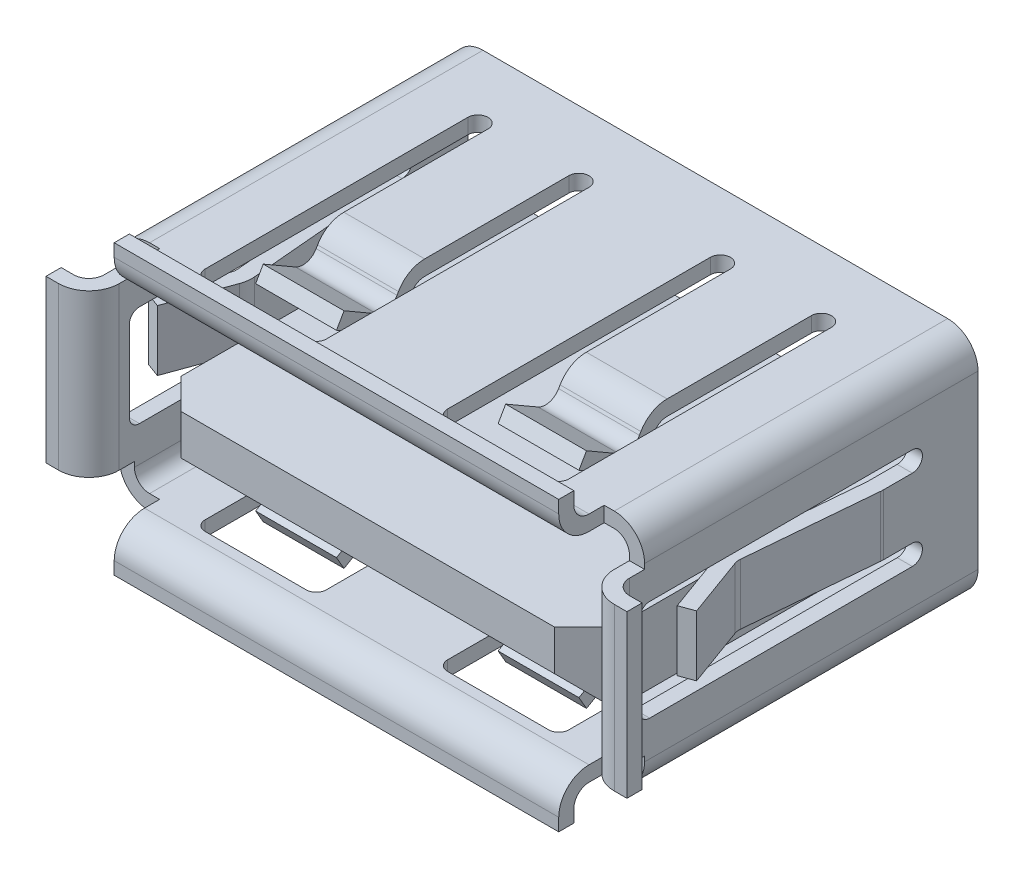
SolidWorks part; units mm, degrees
ref_plane "Front Plane" through (0, 0, 0) normal (0, 0, 1) x (1, 0, 0)
ref_plane "Top Plane" through (0, 0, 0) normal (0, 1, 0) x (1, 0, 0)
ref_plane "Right Plane" through (0, 0, 0) normal (1, 0, 0) x (0, 0, -1)
sketch "Sketch10" plane through (0, 0, 0) normal (0, 0, 1) x (1, 0, 0)
  line L0 (-22.3107, 0) -> (0, 0) construction
  line L1 (0, 8.8149) -> (0, -8.8149) construction
  line L2 (-5.842, 2.54) -> (5.842, 2.54)
  line L3 (-5.842, 2.921) -> (5.842, 2.921)
  line L4 (-6.604, 2.159) -> (-6.604, -2.159)
  line L5 (-5.842, -2.921) -> (5.842, -2.921)
  line L6 (6.604, 2.159) -> (6.604, -2.159)
  line L7 (6.223, 2.159) -> (6.223, -2.159)
  line L8 (-5.842, -2.54) -> (5.842, -2.54)
  line L9 (-6.223, 2.159) -> (-6.223, -2.159)
  arc A0 (-6.604, 2.159) -> (-5.842, 2.921) centre (-5.842, 2.159) cw
  arc A1 (-5.842, -2.921) -> (-6.604, -2.159) centre (-5.842, -2.159) cw
  arc A2 (6.604, -2.159) -> (5.842, -2.921) centre (5.842, -2.159) cw
  arc A3 (5.842, 2.921) -> (6.604, 2.159) centre (5.842, 2.159) cw
  arc A4 (-6.223, 2.159) -> (-5.842, 2.54) centre (-5.842, 2.159) cw
  arc A5 (5.842, 2.54) -> (6.223, 2.159) centre (5.842, 2.159) cw
  arc A6 (6.223, -2.159) -> (5.842, -2.54) centre (5.842, -2.159) cw
  arc A7 (-5.842, -2.54) -> (-6.223, -2.159) centre (-5.842, -2.159) cw
  point P13 (-6.604, -2.921)
  point P16 (6.604, -2.921)
  dimension "D6" = 0.762
  dimension "D2" = 13.208
  dimension "D3" = 6.604
  dimension "D4" = 5.842
  dimension "D5" = 2.921
  dimension "D7" = 0.381
extrude "Extrude6" add sketch "Sketch10" along normal blind 8.382
sketch "Sketch11" plane through (0, 0, 8.382) normal (0, 0, 1) x (1, 0, 0)
  line L0 (-6.604, 2.159) -> (-6.604, -2.159) construction
  line L1 (-6.604, 2.032) -> (-6.223, 2.032)
  line L2 (-6.604, 2.032) -> (-6.604, -2.032)
  line L3 (-6.604, -2.032) -> (-6.223, -2.032)
  line L4 (-6.223, 2.032) -> (-6.223, -2.032)
  line L5 (-6.223, 2.159) -> (-6.223, -2.159) construction
  line L6 (-5.842, -2.54) -> (5.842, -2.54) construction
  line L7 (-5.588, -2.54) -> (5.588, -2.54)
  line L8 (-5.588, -2.54) -> (-5.588, -2.921)
  line L9 (-5.588, -2.921) -> (5.588, -2.921)
  line L10 (5.588, -2.54) -> (5.588, -2.921)
  line L11 (-5.842, -2.921) -> (5.842, -2.921) construction
  line L12 (5.842, 2.921) -> (-5.842, 2.921) construction
  line L13 (-5.588, 2.921) -> (5.588, 2.921)
  line L14 (-5.588, 2.921) -> (-5.588, 2.54)
  line L15 (-5.588, 2.54) -> (5.588, 2.54)
  line L16 (5.588, 2.921) -> (5.588, 2.54)
  line L17 (5.842, 2.54) -> (-5.842, 2.54) construction
  line L18 (6.223, -2.159) -> (6.223, 2.159) construction
  line L19 (6.223, 2.032) -> (6.604, 2.032)
  line L20 (6.223, 2.032) -> (6.223, -2.032)
  line L21 (6.223, -2.032) -> (6.604, -2.032)
  line L22 (6.604, 2.032) -> (6.604, -2.032)
  line L23 (6.604, -2.159) -> (6.604, 2.159) construction
  dimension "D1" = 11.176
  dimension "D2" = 4.064
  dimension "D3" = 0.889
  dimension "D4" = 1.016
extrude "Extrude7" add sketch "Sketch11" along normal blind 0.254
sketch "Sketch12" plane through (5.588, 0, 0) normal (1, 0, 0) x (0, 0, -1)
  line L0 (-9.525, 3.302) -> (-9.525, 3.6195)
  line L1 (-9.144, 3.302) -> (-9.144, 3.6195)
  line L2 (-9.525, 3.6195) -> (-9.144, 3.6195)
  line L3 (-9.525, -3.302) -> (-9.525, -3.6195)
  line L4 (-8.382, 2.54) -> (-8.382, 2.921)
  line L5 (-8.382, 2.921) -> (-8.636, 2.921)
  line L6 (-8.636, 2.921) -> (-8.636, 2.54)
  line L7 (-8.636, 2.54) -> (-8.382, 2.54)
  line L8 (-8.382, 2.54) -> (-8.382, 2.921)
  line L9 (-8.382, 2.921) -> (-8.763, 2.921)
  line L10 (-8.382, -2.921) -> (-8.382, -2.54)
  line L11 (-8.763, 2.54) -> (-8.382, 2.54)
  line L12 (-8.382, -2.54) -> (-8.636, -2.54)
  line L13 (-8.636, -2.54) -> (-8.636, -2.921)
  line L14 (-8.636, -2.921) -> (-8.382, -2.921)
  line L15 (-8.382, -2.921) -> (-8.382, -2.54)
  line L16 (-8.382, -2.54) -> (-8.763, -2.54)
  line L17 (-9.144, -3.302) -> (-9.144, -3.6195)
  line L18 (-8.763, -2.921) -> (-8.382, -2.921)
  line L19 (-9.525, -3.6195) -> (-9.144, -3.6195)
  line L20 (0, 0) -> (-11.5715, 0) construction
  line L21 (0, -2.159) -> (0, 2.159) construction
  arc A0 (-8.763, 2.54) -> (-9.525, 3.302) centre (-8.763, 3.302) cw
  arc A1 (-8.763, -2.54) -> (-9.525, -3.302) centre (-8.763, -3.302) ccw
  arc A2 (-8.763, 2.921) -> (-9.144, 3.302) centre (-8.763, 3.302) cw
  arc A3 (-8.763, -2.921) -> (-9.144, -3.302) centre (-8.763, -3.302) ccw
  dimension "D7" = 0.762
  dimension "D8" = 0.381
  dimension "D3" = 1.0795
  dimension "D4" = 1.0795
  dimension "D5" = 0.381
  dimension "D6" = 9.525
  dimension "D1" = 0
  dimension "D2" = 0
extrude "Extrude8" add sketch "Sketch12" against normal blind 11.176
sketch "Sketch13" plane through (0, 2.032, 0) normal (0, 1, 0) x (-1, 0, 0)
  line L0 (-6.985, 9.144) -> (-7.3025, 9.144)
  line L1 (-7.3025, 9.144) -> (-7.3025, 9.525)
  line L2 (-7.3025, 9.525) -> (-6.985, 9.525)
  line L3 (6.985, 9.144) -> (7.3025, 9.144)
  line L4 (6.223, 8.382) -> (6.604, 8.382)
  line L5 (6.604, 8.382) -> (6.604, 8.636)
  line L6 (6.604, 8.636) -> (6.223, 8.636)
  line L7 (6.223, 8.636) -> (6.223, 8.382)
  line L8 (6.223, 8.382) -> (6.604, 8.382)
  line L9 (6.604, 8.382) -> (6.604, 8.763)
  line L10 (7.3025, 9.144) -> (7.3025, 9.525)
  line L11 (6.223, 8.763) -> (6.223, 8.382)
  line L12 (-6.604, 8.382) -> (-6.223, 8.382)
  line L13 (-6.223, 8.382) -> (-6.223, 8.636)
  line L14 (-6.223, 8.636) -> (-6.604, 8.636)
  line L15 (-6.604, 8.636) -> (-6.604, 8.382)
  line L16 (-6.604, 8.382) -> (-6.223, 8.382)
  line L17 (-6.223, 8.382) -> (-6.223, 8.763)
  line L18 (7.3025, 9.525) -> (6.985, 9.525)
  line L19 (-6.604, 8.763) -> (-6.604, 8.382)
  line L20 (5.588, 9.525) -> (-5.588, 9.525) construction
  arc A0 (-6.985, 9.144) -> (-6.604, 8.763) centre (-6.985, 8.763) cw
  arc A1 (6.985, 9.144) -> (6.604, 8.763) centre (6.985, 8.763) ccw
  arc A2 (-6.223, 8.763) -> (-6.985, 9.525) centre (-6.985, 8.763) ccw
  arc A3 (6.985, 9.525) -> (6.223, 8.763) centre (6.985, 8.763) ccw
  point P26 (6.223, 9.525)
  dimension "D6" = 0.381
  dimension "D7" = 0.762
  dimension "D3" = 0.381
  dimension "D4" = 1.0795
  dimension "D5" = 1.0795
  dimension "D1" = 0
  dimension "D2" = 0
extrude "Extrude9" add sketch "Sketch13" against normal up to surface (4.064 mm away) up to face at (-6.4611, -2.032, 8.5725)
sketch "Sketch14" plane through (0, 2.921, 0) normal (0, 1, 0) x (-1, 0, 0)
  line L0 (0, 0) -> (0, 2.9776) construction
  line L1 (-2.032, 1.651) -> (-2.032, 2.159)
  line L2 (4.572, 1.651) -> (4.572, 8.255)
  line L3 (4.318, 8.509) -> (1.778, 8.509)
  line L4 (1.524, 1.651) -> (1.524, 8.255)
  line L5 (-3.048, 8.509) -> (-3.048, 0.7388) construction
  line L6 (-1.524, 1.651) -> (-1.524, 8.255)
  line L7 (-1.778, 8.509) -> (-4.318, 8.509)
  line L8 (-4.572, 1.651) -> (-4.572, 8.255)
  line L10 (3.048, 8.509) -> (3.048, 0.7388) construction
  line L11 (-2.032, 2.159) -> (-4.064, 2.159)
  line L12 (5.588, 9.525) -> (-5.588, 9.525) construction
  line L13 (-4.064, 2.159) -> (-4.064, 1.651)
  line L14 (4.064, 1.651) -> (4.064, 2.159)
  line L15 (4.064, 2.159) -> (2.032, 2.159)
  line L16 (2.032, 2.159) -> (2.032, 1.651)
  arc A0 (-4.572, 8.255) -> (-4.318, 8.509) centre (-4.318, 8.255) cw
  arc A1 (-1.524, 8.255) -> (-1.778, 8.509) centre (-1.778, 8.255) ccw
  arc A2 (-2.032, 1.651) -> (-1.524, 1.651) centre (-1.778, 1.651) ccw
  arc A3 (-4.572, 1.651) -> (-4.064, 1.651) centre (-4.318, 1.651) ccw
  arc A4 (2.032, 1.651) -> (1.524, 1.651) centre (1.778, 1.651) cw
  arc A5 (4.572, 1.651) -> (4.064, 1.651) centre (4.318, 1.651) cw
  arc A6 (4.318, 8.509) -> (4.572, 8.255) centre (4.318, 8.255) cw
  arc A7 (1.524, 8.255) -> (1.778, 8.509) centre (1.778, 8.255) cw
  dimension "D6" = 7.112
  dimension "D1" = 0.254
  dimension "D7" = 0.762
  dimension "D2" = 1.016
  dimension "D3" = 3.048
  dimension "D4" = 6.096
  dimension "D5" = 3.048
extrude "Cut-Extrude4" cut sketch "Sketch14" against normal up to surface (5.842 mm away) up to face at (0, -2.921, 6.3818)
sketch "Sketch15" plane through (6.604, 0, 0) normal (1, 0, 0) x (0, 0, -1)
  line L0 (0, 0) -> (-4.7284, 0) construction
  line L2 (-9.525, -2.032) -> (-9.525, 2.032) construction
  line L3 (-8.255, 1.27) -> (-1.651, 1.27)
  line L4 (-8.509, 1.016) -> (-8.509, -1.016)
  line L5 (-8.255, -1.27) -> (-1.651, -1.27)
  line L6 (-1.651, 0.762) -> (-1.905, 0.762)
  line L7 (-1.905, 0.762) -> (-1.905, -0.762)
  line L8 (-1.905, -0.762) -> (-1.651, -0.762)
  arc A0 (-8.509, 1.016) -> (-8.255, 1.27) centre (-8.255, 1.016) cw
  arc A1 (-8.255, -1.27) -> (-8.509, -1.016) centre (-8.255, -1.016) cw
  arc A2 (-1.651, -0.762) -> (-1.651, -1.27) centre (-1.651, -1.016) cw
  arc A3 (-1.651, 1.27) -> (-1.651, 0.762) centre (-1.651, 1.016) cw
  point P12 (-8.509, 1.27)
  point P15 (-8.509, -1.27)
  dimension "D5" = 0.254
  dimension "D2" = 7.112
  dimension "D6" = 0.508
  dimension "D1" = 1.016
  dimension "D3" = 1.27
  dimension "D4" = 2.54
extrude "Cut-Extrude5" cut sketch "Sketch15" against normal blind 13.462
sketch "Sketch17" plane through (4.064, 0, 0) normal (1, 0, 0) x (0, 0, -1)
  line L0 (-5.935, 2.54) -> (-5.9716, 2.4765)
  line L1 (-8.509, 2.54) -> (-8.509, 2.921) construction
  line L2 (-6.4921, 2.337) -> (-7.3025, 2.8049)
  line L3 (-5.605, 2.3495) -> (-5.6417, 2.286)
  line L4 (-2.159, 2.54) -> (-1.651, 2.54)
  line L5 (-1.651, 2.54) -> (-1.651, 2.921)
  line L6 (-1.651, 2.921) -> (-2.159, 2.921)
  line L7 (-2.159, 2.921) -> (-2.159, 2.54)
  line L8 (-5.2751, 2.54) -> (-1.651, 2.54)
  line L9 (-1.651, 2.54) -> (-1.651, 2.921)
  line L10 (-1.651, 2.921) -> (-5.2751, 2.921)
  line L11 (-5.2751, 2.921) -> (-5.715, 2.921) construction
  line L12 (-6.6826, 2.0071) -> (-7.493, 2.475)
  line L13 (-7.493, 2.475) -> (-7.3025, 2.8049)
  line L14 (-5.715, 2.921) -> (-5.935, 2.54) construction
  line L15 (-5.6417, -2.286) -> (-5.605, -2.3495)
  line L16 (-6.6826, -2.0071) -> (-7.493, -2.475)
  line L17 (-5.935, -2.54) -> (-5.9716, -2.4765)
  line L18 (-6.4921, -2.337) -> (-7.3025, -2.8049)
  line L19 (-1.651, -2.54) -> (-2.159, -2.54)
  line L20 (-2.159, -2.54) -> (-2.159, -2.921)
  line L21 (-2.159, -2.921) -> (-1.651, -2.921)
  line L22 (-1.651, -2.921) -> (-1.651, -2.54)
  line L23 (-1.651, -2.54) -> (-5.2751, -2.54)
  line L24 (-7.493, -2.475) -> (-7.3025, -2.8049)
  line L25 (-5.2751, -2.921) -> (-1.651, -2.921)
  line L26 (-1.651, -2.921) -> (-1.651, -2.54)
  arc A0 (-6.4921, 2.337) -> (-5.9716, 2.4765) centre (-6.3016, 2.667) ccw
  arc A1 (-6.6826, 2.0071) -> (-5.6417, 2.286) centre (-6.3016, 2.667) ccw
  arc A2 (-5.2751, 2.921) -> (-5.935, 2.54) centre (-5.2751, 2.159) ccw
  arc A3 (-5.2751, 2.54) -> (-5.605, 2.3495) centre (-5.2751, 2.159) ccw
  arc A4 (-5.2751, -2.54) -> (-5.605, -2.3495) centre (-5.2751, -2.159) cw
  arc A5 (-5.9716, -2.4765) -> (-6.4921, -2.337) centre (-6.3016, -2.667) ccw
  arc A6 (-5.2751, -2.921) -> (-5.935, -2.54) centre (-5.2751, -2.159) cw
  arc A7 (-6.6826, -2.0071) -> (-5.6417, -2.286) centre (-6.3016, -2.667) cw
  dimension "D3" = 0.762
  dimension "D7" = 0.762
  dimension "D8" = 0.381
  dimension "D9" = 4.064
  dimension "D12" = 0.381
  dimension "D13" = 0.762
  dimension "D16" = 1.016
  dimension "D2" = 0.381
  dimension "D4" = 60
  dimension "D5" = 1.016
  dimension "D6" = 1.016
  dimension "D10" = 90
  dimension "D14" = 0.381
  dimension "D15" = 0.381
  dimension "D17" = 60
  dimension "D18" = 90
  dimension "D1" = 0
  dimension "D11" = 0
extrude "Extrude10" add sketch "Sketch17" against normal blind 2.032
sketch "Sketch18" plane through (-2.032, 0, 0) normal (1, 0, 0) x (0, 0, -1)
  line L8 (-5.935, 2.54) -> (-5.9716, 2.4765)
  line L9 (-6.4921, 2.337) -> (-7.3025, 2.8049)
  line L10 (-7.3025, 2.8049) -> (-7.493, 2.475)
  line L11 (-7.493, 2.475) -> (-6.6826, 2.0071)
  line L12 (-5.6417, 2.286) -> (-5.605, 2.3495)
  line L13 (-5.2751, 2.54) -> (-1.651, 2.54)
  line L14 (-1.651, 2.54) -> (-1.651, 2.921)
  line L15 (-1.651, 2.921) -> (-5.2751, 2.921)
  line L16 (-5.935, 2.54) -> (-5.9716, 2.4765)
  line L17 (-6.4921, 2.337) -> (-7.3025, 2.8049)
  line L18 (-7.3025, 2.8049) -> (-7.493, 2.475)
  line L19 (-7.493, 2.475) -> (-6.6826, 2.0071)
  line L20 (-5.6417, 2.286) -> (-5.605, 2.3495)
  line L21 (-5.2751, 2.54) -> (-1.651, 2.54)
  line L22 (-1.651, 2.54) -> (-1.651, 2.921)
  line L23 (-1.651, 2.921) -> (-5.2751, 2.921)
  line L24 (-5.605, -2.3495) -> (-5.6417, -2.286)
  line L25 (-1.651, -2.54) -> (-5.2751, -2.54)
  line L26 (-1.651, -2.921) -> (-1.651, -2.54)
  line L27 (-5.2751, -2.921) -> (-1.651, -2.921)
  line L28 (-5.9716, -2.4765) -> (-5.935, -2.54)
  line L29 (-7.3025, -2.8049) -> (-6.4921, -2.337)
  line L30 (-7.493, -2.475) -> (-7.3025, -2.8049)
  line L31 (-6.6826, -2.0071) -> (-7.493, -2.475)
  line L32 (-5.605, -2.3495) -> (-5.6417, -2.286)
  line L33 (-1.651, -2.54) -> (-5.2751, -2.54)
  line L34 (-1.651, -2.921) -> (-1.651, -2.54)
  line L35 (-5.2751, -2.921) -> (-1.651, -2.921)
  line L36 (-5.9716, -2.4765) -> (-5.935, -2.54)
  line L37 (-7.3025, -2.8049) -> (-6.4921, -2.337)
  line L38 (-7.493, -2.475) -> (-7.3025, -2.8049)
  line L39 (-6.6826, -2.0071) -> (-7.493, -2.475)
  arc A4 (-6.4921, 2.337) -> (-5.9716, 2.4765) centre (-6.3016, 2.667) ccw
  arc A5 (-6.6826, 2.0071) -> (-5.6417, 2.286) centre (-6.3016, 2.667) ccw
  arc A6 (-5.2751, 2.54) -> (-5.605, 2.3495) centre (-5.2751, 2.159) ccw
  arc A7 (-5.2751, 2.921) -> (-5.935, 2.54) centre (-5.2751, 2.159) ccw
  arc A8 (-6.4921, 2.337) -> (-5.9716, 2.4765) centre (-6.3016, 2.667) ccw
  arc A9 (-6.6826, 2.0071) -> (-5.6417, 2.286) centre (-6.3016, 2.667) ccw
  arc A10 (-5.2751, 2.54) -> (-5.605, 2.3495) centre (-5.2751, 2.159) ccw
  arc A11 (-5.2751, 2.921) -> (-5.935, 2.54) centre (-5.2751, 2.159) ccw
  arc A12 (-5.605, -2.3495) -> (-5.2751, -2.54) centre (-5.2751, -2.159) ccw
  arc A13 (-5.935, -2.54) -> (-5.2751, -2.921) centre (-5.2751, -2.159) ccw
  arc A14 (-5.9716, -2.4765) -> (-6.4921, -2.337) centre (-6.3016, -2.667) ccw
  arc A15 (-5.6417, -2.286) -> (-6.6826, -2.0071) centre (-6.3016, -2.667) ccw
  arc A16 (-5.605, -2.3495) -> (-5.2751, -2.54) centre (-5.2751, -2.159) ccw
  arc A17 (-5.935, -2.54) -> (-5.2751, -2.921) centre (-5.2751, -2.159) ccw
  arc A18 (-5.9716, -2.4765) -> (-6.4921, -2.337) centre (-6.3016, -2.667) ccw
  arc A19 (-5.6417, -2.286) -> (-6.6826, -2.0071) centre (-6.3016, -2.667) ccw
  dimension "D1" = 0
  dimension "D2" = 0
extrude "Extrude11" add sketch "Sketch18" against normal blind 2.032
sketch "Sketch20" plane through (0, 0.762, 0) normal (0, 1, 0) x (-1, 0, 0)
  line L0 (-6.6011, 2.4461) -> (-6.318, 5.6818)
  line L1 (-6.3395, 5.8453) -> (-6.8918, 7.3627)
  line L2 (-6.223, 2.3964) -> (-5.9385, 5.6486)
  line L3 (-5.9815, 5.9756) -> (-6.5338, 7.493)
  line L4 (-6.223, 1.651) -> (-6.223, 1.905)
  line L5 (-6.223, 1.905) -> (-6.604, 1.905)
  line L6 (-6.604, 1.905) -> (-6.604, 1.651)
  line L7 (-6.604, 1.651) -> (-6.223, 1.651)
  line L8 (-6.223, 1.651) -> (-6.223, 2.3964)
  line L9 (-6.5338, 7.493) -> (-6.8918, 7.3627)
  line L10 (-6.604, 2.3797) -> (-6.604, 1.651)
  line L11 (-6.604, 1.651) -> (-6.223, 1.651)
  line L12 (-6.223, 8.509) -> (-6.604, 8.509) construction
  line L13 (6.6011, 2.4461) -> (6.318, 5.6818)
  line L14 (6.3395, 5.8453) -> (6.8918, 7.3627)
  line L15 (6.223, 2.3964) -> (5.9385, 5.6486)
  line L16 (5.9815, 5.9756) -> (6.5338, 7.493)
  line L17 (6.223, 1.905) -> (6.223, 1.651)
  line L18 (6.223, 1.651) -> (6.604, 1.651)
  line L19 (6.604, 1.651) -> (6.604, 1.905)
  line L20 (6.604, 1.905) -> (6.223, 1.905)
  line L21 (6.223, 2.3964) -> (6.223, 1.651)
  line L22 (6.223, 1.651) -> (6.604, 1.651)
  line L23 (6.604, 1.651) -> (6.604, 2.3797)
  line L24 (6.8918, 7.3627) -> (6.5338, 7.493)
  line L25 (6.604, 8.509) -> (6.223, 8.509) construction
  arc A0 (-6.3395, 5.8453) -> (-6.318, 5.6818) centre (-6.6976, 5.715) cw
  arc A1 (-5.9815, 5.9756) -> (-5.9385, 5.6486) centre (-6.6976, 5.715) cw
  arc A2 (5.9815, 5.9756) -> (5.9385, 5.6486) centre (6.6976, 5.715) ccw
  arc A3 (6.3395, 5.8453) -> (6.318, 5.6818) centre (6.6976, 5.715) ccw
  arc A4 (-6.6011, 2.4461) -> (-6.604, 2.3797) centre (-5.842, 2.3797) ccw
  arc A5 (6.6011, 2.4461) -> (6.604, 2.3797) centre (5.842, 2.3797) cw
  point P34 (-6.604, 2.413)
  point P37 (6.604, 2.413)
  dimension "D6" = 0.381
  dimension "D7" = 0.762
  dimension "D15" = 0.762
  dimension "D16" = 0.381
  dimension "D19" = 4.064
  dimension "D21" = 0.762
  dimension "D2" = 0.762
  dimension "D3" = 5
  dimension "D4" = 0.381
  dimension "D5" = 0.381
  dimension "D8" = 1.016
  dimension "D9" = 25
  dimension "D10" = 4.064
  dimension "D12" = 0.762
  dimension "D13" = 5
  dimension "D14" = 0.381
  dimension "D17" = 1.016
  dimension "D18" = 25
  dimension "D20" = 0.381
  dimension "D1" = 0
  dimension "D11" = 0
extrude "Extrude12" add sketch "Sketch20" against normal blind 1.524
sketch "Sketch21" plane through (0, 0, 0) normal (0, 0, 1) x (1, 0, 0)
  line L1 (-5.461, -1.778) -> (5.461, -1.778)
  line L2 (-5.461, -1.778) -> (-5.461, 0)
  line L3 (-5.461, 0) -> (5.461, 0)
  line L4 (5.461, -1.778) -> (5.461, 0)
  line L6 (-5.842, -2.54) -> (5.842, -2.54) construction
  line L8 (6.223, -2.159) -> (6.223, 2.159) construction
  line L9 (-6.223, 2.159) -> (-6.223, -2.159) construction
  dimension "D1" = 0.762
  dimension "D2" = 0.762
  dimension "D3" = 0.762
  dimension "D4" = 1.778
extrude "Extrude14" add sketch "Sketch21" along normal blind 8.7376
chamfer "Chamfer2" distance 0.762 angle 45 2 edges at (-5.461, -0.889, 8.7376) (0, -1.778, 8.7376)
